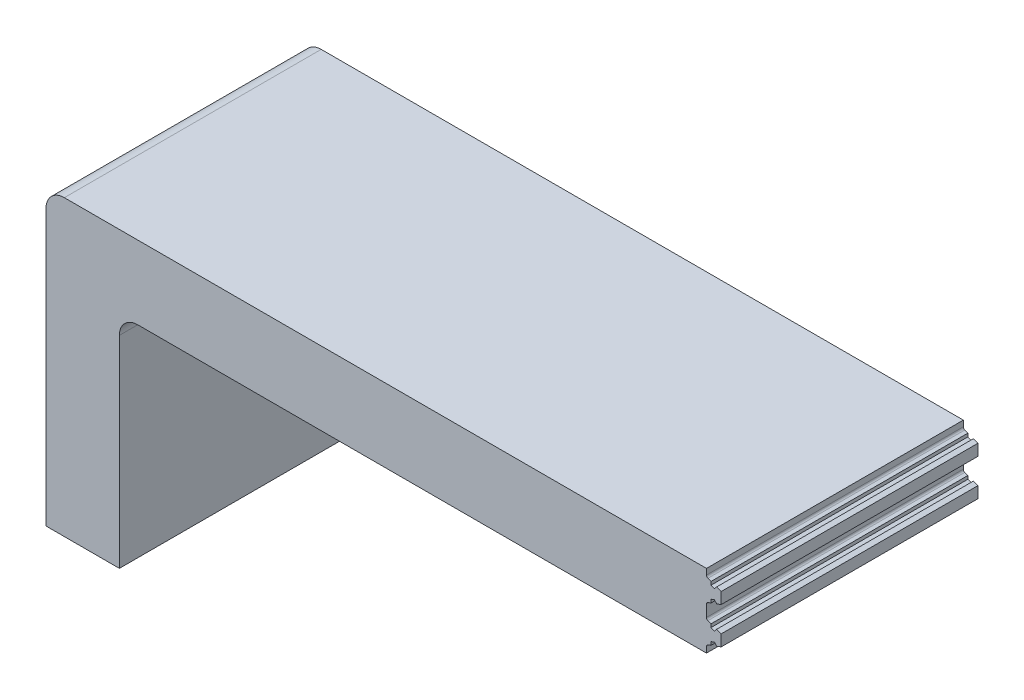
SolidWorks part; units mm, degrees
ref_plane "Front Plane" through (0, 0, 0) normal (0, 0, 1) x (1, 0, 0)
ref_plane "Top Plane" through (0, 0, 0) normal (0, 1, 0) x (1, 0, 0)
ref_plane "Right Plane" through (0, 0, 0) normal (1, 0, 0) x (0, 0, -1)
sketch "Sketch1" plane through (0, 0, 0) normal (0, 0, 1) x (1, 0, 0)
  line L0 (0, 0) -> (0, 101.6)
  line L6 (25.4, 76.2) -> (25.4, 0)
  line L7 (25.4, 0) -> (0, 0)
  line L8 (0, 101.6) -> (233.68, 101.6)
  line L10 (233.68, 76.2) -> (25.4, 76.2)
  line L14 (233.68, 76.2) -> (233.68, 101.6)
  dimension "D1" = 101.6
  dimension "D2" = 25.4
  dimension "D3" = 25.4
  dimension "D4" = 233.68
extrude "Boss-Extrude2" add sketch "Sketch1" along normal blind 88.9
sketch "Sketch8" plane through (0, 0, 88.9) normal (0, 0, 1) x (1, 0, 0)
  line L0 (228.6, 76.2) -> (228.6, 78.74)
  line L3 (25.4, 76.2) -> (233.68, 76.2) construction
  line L4 (233.68, 101.6) -> (0, 101.6) construction
  line L5 (228.6, 101.6) -> (233.68, 101.6)
  line L7 (233.68, 76.2) -> (228.6, 76.2)
  line L8 (233.68, 88.9) -> (228.6, 88.9) construction
  line L10 (228.6, 78.74) -> (230.1785, 79.3145)
  line L11 (228.6, 86.36) -> (228.6, 91.44)
  line L12 (233.68, 80.589) -> (233.68, 76.2)
  line L14 (233.68, 93.289) -> (233.68, 84.511)
  line L15 (231.14, 79.6645) -> (230.7752, 80.6668) construction
  line L16 (230.1785, 79.3145) -> (230.1785, 80.4497)
  line L17 (230.1785, 80.4497) -> (231.3719, 80.884)
  line L18 (232.1015, 80.0145) -> (231.3719, 80.884)
  line L19 (232.1015, 80.0145) -> (233.68, 80.589)
  line L20 (232.1015, 97.7855) -> (231.3719, 96.916)
  line L21 (233.68, 82.55) -> (228.6, 82.55) construction
  line L22 (233.68, 76.2) -> (233.68, 101.6) construction
  line L23 (232.1015, 85.0855) -> (233.68, 84.511)
  line L24 (232.1015, 85.0855) -> (231.3719, 84.216)
  line L25 (230.1785, 84.6503) -> (231.3719, 84.216)
  line L26 (230.1785, 85.7855) -> (230.1785, 84.6503)
  line L27 (228.6, 86.36) -> (230.1785, 85.7855)
  line L28 (232.1015, 97.7855) -> (233.68, 97.211)
  line L29 (230.1785, 97.3503) -> (231.3719, 96.916)
  line L30 (230.1785, 98.4855) -> (230.1785, 97.3503)
  line L31 (228.6, 99.06) -> (230.1785, 98.4855)
  line L32 (232.1015, 92.7145) -> (233.68, 93.289)
  line L33 (232.1015, 92.7145) -> (231.3719, 93.584)
  line L34 (230.1785, 93.1497) -> (231.3719, 93.584)
  line L35 (230.1785, 92.0145) -> (230.1785, 93.1497)
  line L36 (228.6, 91.44) -> (230.1785, 92.0145)
  line L37 (228.6, 101.6) -> (228.6, 99.06)
  line L38 (233.68, 101.6) -> (233.68, 97.211)
  dimension "D1" = 5.08
  dimension "D3" = 2.54
  dimension "D6" = 0.635
extrude "Cut-Extrude3" cut sketch "Sketch8" against normal through all
fillet "Fillet2" radius 6.35 2 edges at (25.4, 76.2, 44.45) (0, 101.6, 44.45)
fillet "Fillet4" radius 0.762 4 edges at (228.6, 99.06, 44.45) (228.6, 91.44, 44.45) (228.6, 86.36, 44.45) (228.6, 78.74, 44.45)
